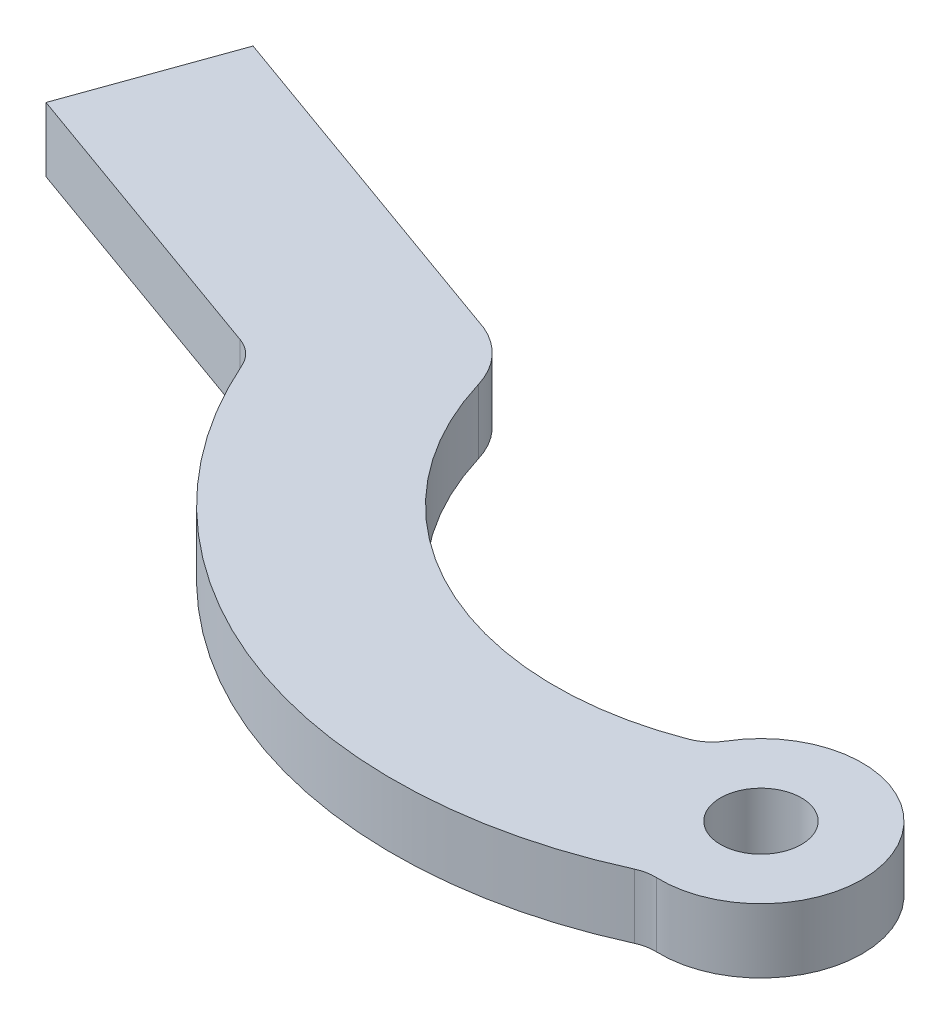
SolidWorks part; units mm, degrees
ref_plane "Front Plane" through (0, 0, 0) normal (0, 0, 1) x (1, 0, 0)
ref_plane "Top Plane" through (0, 0, 0) normal (0, 1, 0) x (1, 0, 0)
ref_plane "Right Plane" through (0, 0, 0) normal (1, 0, 0) x (0, 0, -1)
sketch "Sketch1" plane through (0, 0, 0) normal (0, 1, 0) x (1, 0, 0)
  line L0 (0, 0) -> (-283.949, 101.6936) construction
  line L1 (0, 0) -> (-23.5361, 8.4292) construction
  line L2 (-13.9826, 7.1321) -> (-22.8618, 10.3121)
  line L3 (-16.7382, 3.8702) -> (-24.2104, 6.5463)
  line L4 (-22.8618, 10.3121) -> (-24.2104, 6.5463)
  line L5 (0.6743, 1.8829) -> (-22.8618, 10.3121) construction
  line L6 (-0.6743, -1.8829) -> (-24.2104, 6.5463) construction
  line L12 (-213.7381, 76.5482) -> (-283.2244, 103.5577)
  circle A0 centre (0, 0) radius 1
  arc A1 (-0.0888, -2.4984) -> (-0.4898, 2.4516) centre (0, 0) ccw
  arc A2 (-2.6433, 0.8636) -> (-2.1456, 1.2831) centre (-3.0038, 1.7964) ccw
  arc A3 (-0.0888, -2.4984) -> (-0.5412, -2.5888) centre (-0.1244, -3.4978) ccw
  arc A4 (-16.1607, 3.333) -> (-16.7382, 3.8702) centre (-17.0754, 2.9288) ccw
  arc A5 (-16.1607, 3.333) -> (-0.5412, -2.5888) centre (-5.4307, 8.0746) ccw
  arc A6 (-12.8369, 5.8572) -> (-2.6433, 0.8636) centre (-5.4307, 8.0746) ccw
  arc A7 (-0.0888, -2.4984) -> (-2.1456, 1.2831) centre (0, 0) ccw
  arc A8 (-12.8369, 5.8572) -> (-13.9826, 7.1321) centre (-14.7596, 5.2816) ccw
  dimension "D1" = 2
  dimension "D3" = 1
  dimension "D4" = 1
  dimension "D2" = 2
  dimension "D6" = 1
  dimension "D5" = 301.61
extrude "Boss-Extrude1" add sketch "Sketch1" along normal blind 1.59
